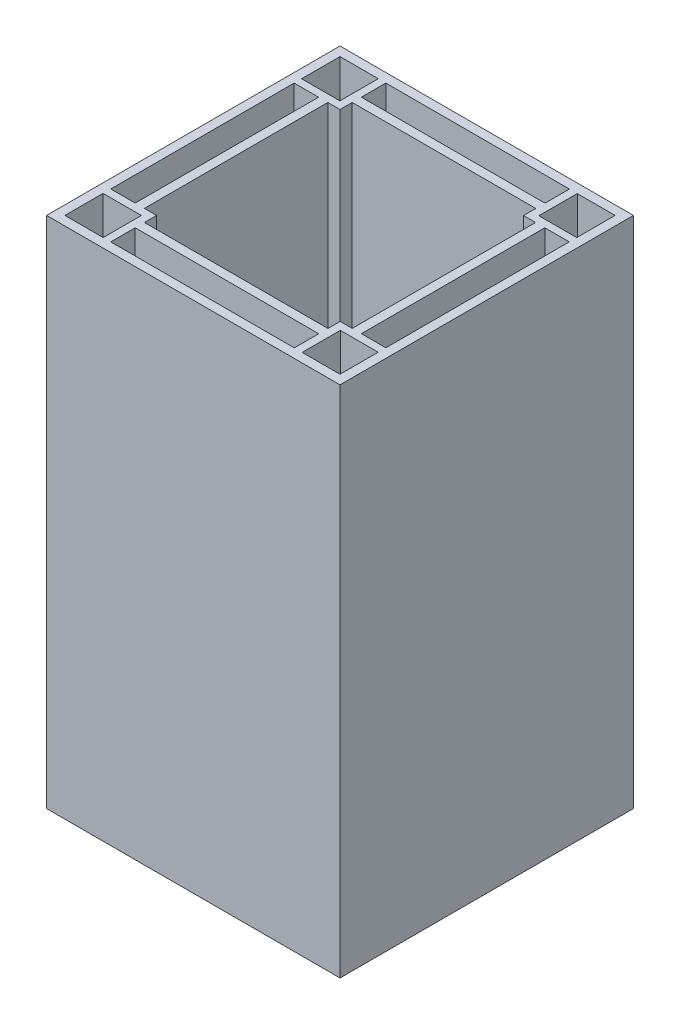
SolidWorks part; units mm, degrees
ref_plane "Front Plane" through (0, 0, 0) normal (0, 0, 1) x (1, 0, 0)
ref_plane "Top Plane" through (0, 0, 0) normal (0, 1, 0) x (1, 0, 0)
ref_plane "Right Plane" through (0, 0, 0) normal (1, 0, 0) x (0, 0, -1)
sketch "Sketch1" plane through (0, 0, 0) normal (1, 0, 0) x (0, 0, -1)
  line L1 (-50.8, -101.6) -> (50.8, -101.6)
  line L2 (-50.8, -101.6) -> (-50.8, 101.6)
  line L3 (-50.8, 101.6) -> (50.8, 101.6)
  line L4 (50.8, -101.6) -> (50.8, 101.6)
  line L5 (-50.8, -101.6) -> (50.8, 101.6) construction
  line L6 (-50.8, 101.6) -> (50.8, -101.6) construction
  point P0 (0, 0)
extrude "Boss-Extrude1" add sketch "Sketch1" along normal blind 101.6
sketch "Sketch2" plane through (0, 101.6, 0) normal (0, 1, 0) x (1, 0, 0)
  line L0 (101.6, 50.8) -> (0, 50.8) construction
  line L1 (3.175, 47.625) -> (15.875, 47.625)
  line L2 (3.175, 47.625) -> (3.175, 34.925)
  line L3 (3.175, 34.925) -> (15.875, 34.925)
  line L4 (15.875, 47.625) -> (15.875, 34.925)
  line L5 (0, 50.8) -> (0, -50.8) construction
  line L6 (101.6, -50.8) -> (0, -50.8) construction
  line L7 (3.175, -34.925) -> (15.875, -34.925)
  line L8 (3.175, -34.925) -> (3.175, -47.625)
  line L9 (3.175, -47.625) -> (15.875, -47.625)
  line L10 (15.875, -34.925) -> (15.875, -47.625)
  line L11 (101.6, 50.8) -> (101.6, -50.8) construction
  line L12 (85.7769, -34.925) -> (98.425, -34.925)
  line L13 (85.7769, -34.925) -> (85.7769, -47.625)
  line L14 (85.7769, -47.625) -> (98.425, -47.625)
  line L15 (98.425, -34.925) -> (98.425, -47.625)
  line L17 (98.425, 47.625) -> (85.7769, 47.625)
  line L18 (98.425, 47.625) -> (98.425, 34.925)
  line L19 (98.425, 34.925) -> (85.7769, 34.925)
  line L20 (85.7769, 47.625) -> (85.7769, 34.925)
  dimension "D1" = 3.175
  dimension "D2" = 3.175
  dimension "D3" = 12.7
  dimension "D4" = 12.7
  dimension "D5" = 3.175
  dimension "D6" = 3.175
  dimension "D7" = 12.7
  dimension "D8" = 12.7
  dimension "D9" = 3.175
extrude "Cut-Extrude1" cut sketch "Sketch2" against normal blind 203.2
sketch "Sketch3" plane through (0, 101.6, 0) normal (0, 1, 0) x (1, 0, 0)
  line L0 (0, 50.8) -> (0, -50.8) construction
  line L1 (3.175, -31.75) -> (11.6408, -31.75)
  line L2 (3.175, -31.75) -> (3.175, 31.75)
  line L3 (3.175, 31.75) -> (11.6408, 31.75)
  line L4 (11.6408, -31.75) -> (11.6408, 31.75)
  line L5 (19.05, 47.625) -> (82.6019, 47.625)
  line L6 (19.05, 47.625) -> (19.05, 39.1592)
  line L7 (19.05, 39.1592) -> (82.6019, 39.1592)
  line L8 (82.6019, 47.625) -> (82.6019, 39.1592)
  line L9 (101.6, 50.8) -> (0, 50.8) construction
  line L10 (15.875, -34.925) -> (3.175, -34.925) construction
  line L11 (3.175, 34.925) -> (15.875, 34.925) construction
  line L12 (15.875, 34.925) -> (15.875, 47.625) construction
  line L13 (85.7769, 47.625) -> (85.7769, 34.925) construction
  line L14 (101.6, 50.8) -> (101.6, -50.8) construction
  line L15 (98.425, 31.75) -> (89.9584, 31.75)
  line L16 (98.425, 31.75) -> (98.425, -31.75)
  line L17 (98.425, -31.75) -> (89.9584, -31.75)
  line L18 (89.9584, 31.75) -> (89.9584, -31.75)
  line L19 (19.05, -39.1592) -> (82.6019, -39.1592)
  line L20 (19.05, -39.1592) -> (19.05, -47.625)
  line L21 (19.05, -47.625) -> (82.6019, -47.625)
  line L22 (82.6019, -39.1592) -> (82.6019, -47.625)
  line L23 (101.6, -50.8) -> (0, -50.8) construction
  line L25 (19.05, 35.9842) -> (82.6019, 35.9842)
  line L26 (19.05, 35.9842) -> (19.05, -35.9842)
  line L27 (19.05, -35.9842) -> (82.6019, -35.9842)
  line L28 (82.6019, 35.9842) -> (82.6019, -35.9842)
  line L29 (14.8158, 31.75) -> (86.7834, 31.75)
  line L30 (14.8158, 31.75) -> (14.8158, -31.75)
  line L31 (14.8158, -31.75) -> (86.7834, -31.75)
  line L32 (86.7834, 31.75) -> (86.7834, -31.75)
  dimension "D1" = 3.175
  dimension "D2" = 3.175
  dimension "D3" = 3.175
  dimension "D4" = 3.175
  dimension "D5" = 3.175
  dimension "D6" = 3.175
  dimension "D7" = 8.4658
  dimension "D8" = 8.4658
  dimension ".3333" = 8.4658
  dimension "D9" = 8.4666
  dimension "D10" = 3.175
  dimension "D11" = 3.175
  dimension "D12" = 3.175
  dimension "D13" = 3.175
  dimension "D14" = 3.175
  dimension ".125" = 3.175
extrude "Cut-Extrude2" cut sketch "Sketch3" against normal blind 200.025 contours L30 L31 L26 L29 | L26 L31 L28 L29 | L26 L29 L28 L25 | L32 L29 L28 L31 | L15 L18 L17 L16 | L8 L5 L6 L7 | L1 L4 L3 L2 | L22 L19 L20 L21 | L31 L26 L27 L28
sketch "Sketch4" plane through (101.6, 0, 0) normal (1, 0, 0) x (0, 0, -1)
  line L0 (50.8, -101.6) -> (50.8, 101.6) construction
  line L1 (-50.8, 101.6) -> (50.8, 101.6)
  line L2 (-50.8, 101.6) -> (-50.8, 76.258)
  line L3 (-50.8, 76.258) -> (50.8, 76.258)
  line L4 (50.8, 101.6) -> (50.8, 76.258)
extrude "Cut-Extrude3" cut sketch "Sketch4" against normal blind 101.6
hole_wizard "1/2-13 Tapped Hole2" positions "3DSketch1" profile "Sketch6" tap size "1/2-13" standard "ANSI Inch" end condition through all
sketch3d "3DSketch1"
  line L0 (14.8158, -98.425, 0) -> (88.5333, -98.425, 0) construction
  line L1 (14.8158, -98.425, -31.75) -> (14.8158, -98.425, 31.75) construction
  line L2 (50.826, -98.425, 35.9842) -> (50.826, -98.425, -41.058) construction
  line L3 (19.05, -98.425, 35.9842) -> (82.6019, -98.425, 35.9842) construction
  point P0 (50.826, -98.425, 0)
  dimension "D1" = 0
  dimension "D2" = 0
sketch "Sketch6" plane through (50.826, -98.425, 0) normal (1, 0, 0) x (0, 0, 1)
  line L0 (0, 0) -> (0, 3.175)
  line L1 (0, 3.175) -> (5.3581, 3.175)
  line L2 (5.3581, 3.175) -> (5.3581, 0)
  line L5 (5.3581, 0) -> (0, 0)
  line L11 (0, -6.35) -> (0, 107.95) construction
  dimension "Thru Tap Drill Dia." = 10.7163
  dimension "Thru Tap Drill Depth" = 3.175
cosmetic thread "Hole Thread1" parameters "D2"=12.7
sketch "Sketch7" plane through (0, 76.258, 0) normal (0, 1, 0) x (1, 0, 0)
  line L1 (3.175, 47.625) -> (16.4308, 47.625)
  line L2 (3.175, 47.625) -> (3.175, 34.3314)
  line L3 (3.175, 34.3314) -> (16.4308, 34.3314)
  line L4 (16.4308, 47.625) -> (16.4308, 34.3314)
  line L5 (98.425, 47.625) -> (85.3206, 47.625)
  line L6 (98.425, 47.625) -> (98.425, 34.3314)
  line L7 (98.425, 34.3314) -> (85.3206, 34.3314)
  line L8 (85.3206, 47.625) -> (85.3206, 34.3314)
  line L9 (98.425, -47.625) -> (85.3206, -47.625)
  line L10 (98.425, -47.625) -> (98.425, -34.4071)
  line L11 (98.425, -34.4071) -> (85.3206, -34.4071)
  line L12 (85.3206, -47.625) -> (85.3206, -34.4071)
  line L13 (3.175, -47.625) -> (16.4308, -47.625)
  line L14 (3.175, -47.625) -> (3.175, -34.4071)
  line L15 (3.175, -34.4071) -> (16.4308, -34.4071)
  line L16 (16.4308, -47.625) -> (16.4308, -34.4071)
extrude "Cut-Extrude4" cut sketch "Sketch7" against normal blind 190.5
